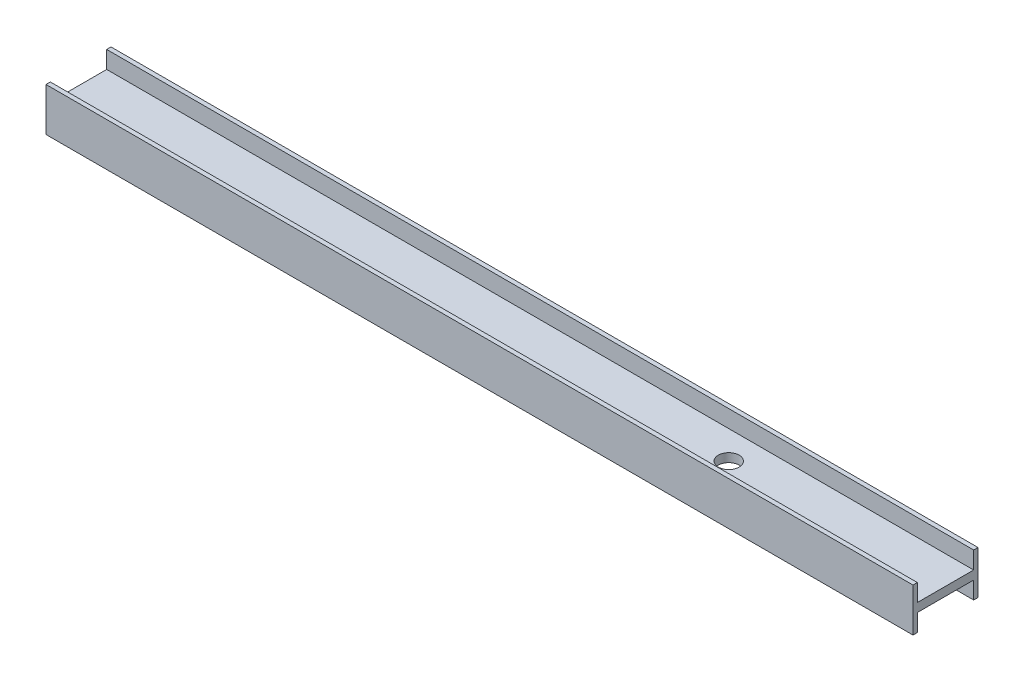
SolidWorks part; units mm, degrees
ref_plane "Front Plane" through (0, 0, 0) normal (0, 0, 1) x (1, 0, 0)
ref_plane "Top Plane" through (0, 0, 0) normal (0, 1, 0) x (1, 0, 0)
ref_plane "Right Plane" through (0, 0, 0) normal (1, 0, 0) x (0, 0, -1)
sketch "Sketch1" plane through (0, 0, 0) normal (0, 1, 0) x (1, 0, 0)
  line L1 (-77.5369, -2.4019) -> (122.4631, -2.4019)
  line L2 (-77.5369, -2.4019) -> (-77.5369, -17.4019)
  line L3 (-77.5369, -17.4019) -> (122.4631, -17.4019)
  line L4 (122.4631, -2.4019) -> (122.4631, -17.4019)
extrude "Boss-Extrude1" add sketch "Sketch1" along normal blind 10
sketch "Sketch3" plane through (0, 10, 0) normal (0, 1, 0) x (1, 0, 0)
  line L0 (-77.5369, -16.4019) -> (122.4631, -16.4019)
  line L1 (-77.5369, -2.4019) -> (-77.5369, -17.4019) construction
  line L2 (122.4631, -17.4019) -> (122.4631, -2.4019) construction
  line L3 (-77.5369, -16.4019) -> (-77.5369, -17.4019)
  line L5 (122.4631, -3.4019) -> (-77.5369, -3.4019)
  line L6 (-77.5369, -16.4019) -> (-77.5369, -3.4547)
  line L7 (122.4631, -16.4019) -> (122.4631, -3.5417)
  line M1 (-77.5369, -2.4019) -> (-77.5369, -17.4019)
  line M3 (122.4631, -17.4019) -> (122.4631, -2.4019)
extrude "Cut-Extrude1" cut sketch "Sketch3" against normal blind 4 contours L5 L0 M3 M1
sketch "Sketch4" plane through (0, 0, 0) normal (0, -1, 0) x (1, 0, 0)
  line L0 (122.4631, 17.4019) -> (122.4631, 16.4019)
  line L1 (122.4631, 17.4019) -> (122.4631, 2.4019) construction
  line L2 (122.4631, 16.4019) -> (-77.5369, 16.4019)
  line L3 (-77.5369, 2.4019) -> (-77.5369, 17.4019) construction
  line L4 (-77.5369, 16.4019) -> (-77.5369, 3.4019)
  line L5 (-77.5369, 3.4019) -> (122.4631, 3.4019)
  line L6 (122.4631, 3.4019) -> (122.4631, 16.4019)
  line L7 (122.4631, 16.4019) -> (122.4336, 16.1821)
extrude "Cut-Extrude2" cut sketch "Sketch4" against normal blind 4
sketch "Sketch5" plane through (0, 4, 0) normal (0, -1, 0) x (-1, 0, 0)
  circle A0 centre (-72.4631, -9.9019) radius 2.4
extrude "Cut-Extrude3" cut sketch "Sketch5" against normal blind 10
